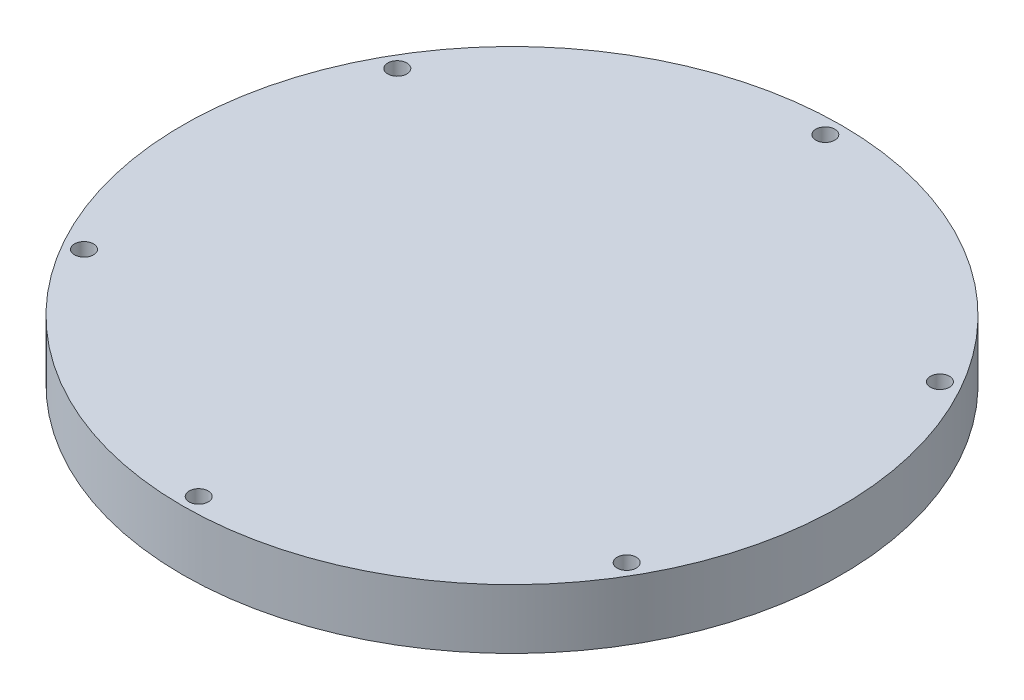
SolidWorks part; units mm, degrees
ref_plane "前视" through (0, 0, 0) normal (0, 0, 1) x (1, 0, 0)
ref_plane "上视" through (0, 0, 0) normal (0, 1, 0) x (1, 0, 0)
ref_plane "右视" through (0, 0, 0) normal (1, 0, 0) x (0, 0, -1)
sketch "草图1" plane through (0, 0, 0) normal (0, 1, 0) x (1, 0, 0)
  circle A0 centre (0, 0) radius 55.25
extrude "凸台-拉伸1" add sketch "草图1" along normal blind 10
sketch "草图3" plane through (0, 10, 0) normal (0, 1, 0) x (1, 0, 0)
  line L0 (0, 0) -> (0, 52.525) construction
  circle A0 centre (0, 0) radius 52.525
  circle A1 centre (0, 52.525) radius 1.6
  circle A2 centre (45.488, 26.2625) radius 1.6
  circle A3 centre (45.488, -26.2625) radius 1.6
  circle A4 centre (0, -52.525) radius 1.6
  circle A5 centre (-45.488, -26.2625) radius 1.6
  circle A6 centre (-45.488, 26.2625) radius 1.6
  point P18 (0, 0)
  dimension "D1" = 6
hole_wizard "Ø3.2 (3.2) 直径孔1" positions "3D草图1" profile "草图4" hole size "Ø3.2" standard "ANSI Metric" end condition through all
sketch3d "3D草图1"
  point P0 (0, 10, -52.525)
  point P3 (-45.488, 10, -26.2625)
  point P6 (-45.488, 10, 26.2625)
  point P9 (0, 10, 52.525)
  point P12 (45.488, 10, 26.2625)
  point P15 (45.488, 10, -26.2625)
sketch "草图4" plane through (0, 10, -52.525) normal (1, 0, 0) x (0, 0, 1)
  line L0 (0, 0) -> (0, 10)
  line L1 (0, 10) -> (1.6, 10)
  line L2 (1.6, 10) -> (1.6, 0)
  line L5 (1.6, 0) -> (0, 0)
  line L11 (0, -6.35) -> (0, 107.95) construction
  dimension "通孔孔直径" = 3.2
  dimension "通孔孔深度" = 10
